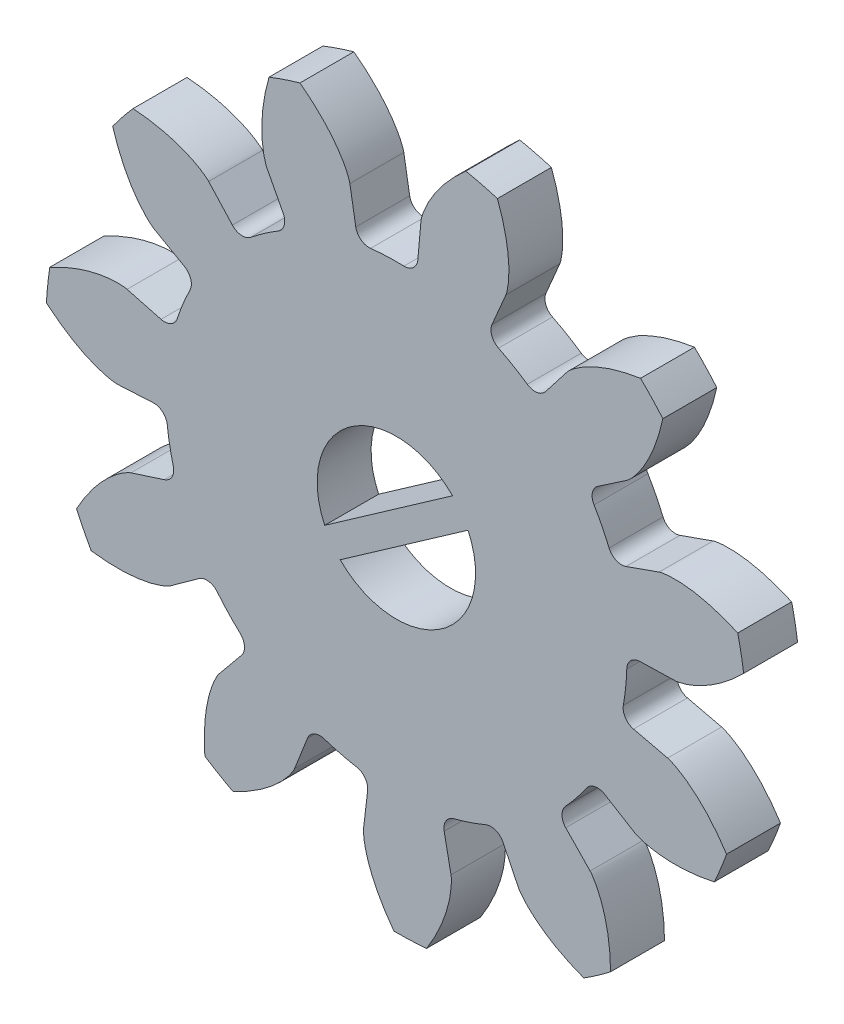
SolidWorks part; units mm, degrees
ref_plane "Front Plane" through (0, 0, 0) normal (0, 0, 1) x (1, 0, 0)
ref_plane "Top Plane" through (0, 0, 0) normal (0, 1, 0) x (1, 0, 0)
ref_plane "Right Plane" through (0, 0, 0) normal (1, 0, 0) x (0, 0, -1)
sketch "Model" plane through (0, 0, 0) normal (0, 0, 1) x (1, 0, 0)
  line L0 (-44.9299, -28.2476) -> (-49.6722, -31.5682)
  line L1 (-49.0986, -32.3873) -> (-44.3563, -29.0667)
  line L2 (-40.6814, -22.148) -> (-41.4798, -23.1761)
  line L3 (-37.9821, -30.0949) -> (-36.6808, -30.0615)
  line L4 (-37.2699, -26.8686) -> (-38.4974, -27.3019)
  line L5 (-39.5362, -25.2471) -> (-38.4595, -24.5155)
  line L6 (-43.4646, -22.0091) -> (-42.9544, -20.8115)
  line L7 (-53.0972, -23.6372) -> (-53.9746, -22.6755)
  line L8 (-55.7432, -27.9864) -> (-57.0012, -27.6517)
  line L9 (-51.8147, -21.1631) -> (-51.2111, -22.3165)
  line L10 (-56.0018, -25.2117) -> (-54.8705, -25.8556)
  line L11 (-55.3922, -36.3718) -> (-54.3365, -35.6103)
  line L12 (-48.0793, -39.2893) -> (-48.2315, -40.5821)
  line L13 (-46.1034, -20.021) -> (-46.2192, -21.3176)
  line L14 (-52.7608, -37.2892) -> (-53.5878, -38.2945)
  line L15 (-50.789, -39.9402) -> (-50.3126, -38.7287)
  line L16 (-55.6178, -33.0756) -> (-56.857, -33.4743)
  line L17 (-57.3355, -30.8812) -> (-56.0356, -30.8114)
  line L18 (-44.9873, -40.4534) -> (-45.2415, -39.1767)
  line L19 (-48.52, -21.4089) -> (-48.7382, -20.1256)
  line L20 (-36.9522, -32.6843) -> (-38.2191, -32.3851)
  line L21 (-39.8292, -37.7485) -> (-40.7332, -36.8119)
  line L22 (-43.0597, -38.4409) -> (-42.4888, -39.6108)
  line L23 (-39.2956, -35.0133) -> (-38.1828, -35.6888)
  arc A0 (-34.1341, -28.5564) -> (-34.3538, -27.3658) centre (-47.0142, -30.3174) ccw
  arc A1 (-39.1252, -27.0231) -> (-38.4974, -27.3019) centre (-38.6639, -26.8304) ccw
  arc A2 (-39.5362, -25.2471) -> (-39.6839, -25.9179) centre (-39.2552, -25.6606) ccw
  arc A3 (-39.1252, -27.0231) -> (-39.6839, -25.9179) centre (-47.0142, -30.3174) ccw
  arc A4 (-37.1309, -21.8724) -> (-37.9593, -20.9896) centre (-47.0142, -30.3174) ccw
  arc A5 (-42.1587, -23.2809) -> (-41.4798, -23.1761) centre (-41.8747, -22.8694) ccw
  arc A6 (-37.9821, -30.0949) -> (-38.469, -30.5794) centre (-37.9693, -30.5947) ccw
  arc A7 (-38.5965, -31.8112) -> (-38.469, -30.5794) centre (-47.0142, -30.3174) ccw
  arc A8 (-43.2655, -17.8697) -> (-44.4398, -17.5749) centre (-47.0142, -30.3174) ccw
  arc A9 (-43.4646, -22.0091) -> (-43.2262, -22.6533) centre (-43.0046, -22.205) ccw
  arc A10 (-54.6701, -26.5127) -> (-55.1395, -27.6587) centre (-47.0142, -30.3174) ccw
  arc A11 (-58.8765, -35.6359) -> (-58.3303, -36.7164) centre (-47.0142, -30.3174) ccw
  arc A12 (-53.0972, -23.6372) -> (-52.4122, -23.6879) centre (-52.7279, -23.3002) ccw
  arc A13 (-55.7432, -27.9864) -> (-55.1395, -27.6587) centre (-55.6147, -27.5032) ccw
  arc A14 (-49.6907, -38.4369) -> (-48.4896, -38.7384) centre (-47.0142, -30.3174) ccw
  arc A15 (-49.6907, -38.4369) -> (-50.3126, -38.7287) centre (-49.8472, -38.9117) ccw
  arc A16 (-51.3978, -22.9776) -> (-52.4122, -23.6879) centre (-47.0142, -30.3174) ccw
  arc A17 (-55.5118, -31.2558) -> (-55.2871, -32.4736) centre (-47.0142, -30.3174) ccw
  arc A18 (-55.5118, -31.2558) -> (-56.0356, -30.8114) centre (-56.0088, -31.3106) ccw
  arc A19 (-48.52, -21.4089) -> (-47.9711, -21.822) centre (-48.027, -21.3251) ccw
  arc A20 (-43.0597, -38.4409) -> (-43.7027, -38.1992) centre (-43.509, -38.6602) ccw
  arc A21 (-42.1587, -23.2809) -> (-43.2262, -22.6533) centre (-47.0142, -30.3174) ccw
  arc A22 (-46.7337, -21.7728) -> (-46.2192, -21.3176) centre (-46.7173, -21.2731) ccw
  arc A23 (-50.5904, -17.819) -> (-51.7376, -18.2059) centre (-47.0142, -30.3174) ccw
  arc A24 (-54.118, -41.2049) -> (-53.0744, -41.8185) centre (-47.0142, -30.3174) ccw
  arc A25 (-55.6178, -33.0756) -> (-55.2871, -32.4736) centre (-55.7709, -32.5997) ccw
  arc A26 (-48.0793, -39.2893) -> (-48.4896, -38.7384) centre (-48.5759, -39.2309) ccw
  arc A27 (-53.6555, -35.7009) -> (-54.3365, -35.6103) centre (-54.0439, -36.0158) ccw
  arc A28 (-56.7799, -21.7365) -> (-57.5358, -22.6822) centre (-47.0142, -30.3174) ccw
  arc A29 (-52.7608, -37.2892) -> (-52.8081, -36.6039) centre (-53.147, -36.9716) ccw
  arc A30 (-46.7337, -21.7728) -> (-47.9711, -21.822) centre (-47.0142, -30.3174) ccw
  arc A31 (-53.6555, -35.7009) -> (-52.8081, -36.6039) centre (-47.0142, -30.3174) ccw
  arc A32 (-51.3978, -22.9776) -> (-51.2111, -22.3165) centre (-51.6541, -22.5483) ccw
  arc A33 (-54.6701, -26.5127) -> (-54.8705, -25.8556) centre (-55.1179, -26.2902) ccw
  arc A34 (-59.8688, -28.3784) -> (-59.9934, -29.5827) centre (-47.0142, -30.3174) ccw
  arc A35 (-44.8761, -38.595) -> (-45.2415, -39.1767) centre (-44.7511, -39.0791) ccw
  arc A36 (-35.2266, -35.7995) -> (-34.7678, -34.6791) centre (-47.0142, -30.3174) ccw
  arc A37 (-40.0617, -41.3021) -> (-39.07, -40.6077) centre (-47.0142, -30.3174) ccw
  arc A38 (-44.8761, -38.595) -> (-43.7027, -38.1992) centre (-47.0142, -30.3174) ccw
  arc A39 (-40.7404, -36.125) -> (-39.9672, -35.1577) centre (-47.0142, -30.3174) ccw
  arc A40 (-40.7404, -36.125) -> (-40.7332, -36.8119) centre (-40.3735, -36.4646) ccw
  arc A41 (-39.2956, -35.0133) -> (-39.9672, -35.1577) centre (-39.555, -35.4408) ccw
  arc A42 (-47.1041, -43.3171) -> (-45.8944, -43.2691) centre (-47.0142, -30.3174) ccw
  arc A43 (-38.5965, -31.8112) -> (-38.2191, -32.3851) centre (-38.1042, -31.8985) ccw
  arc A44 (-44.9299, -28.2476) -> (-49.6722, -31.5682) centre (-47.0142, -30.3174) ccw
  arc A45 (-49.0986, -32.3873) -> (-44.3563, -29.0667) centre (-47.0142, -30.3174) ccw
  spline S0 degree 5 poles (-36.6808, -30.0615) (-36.649, -30.0607) (-36.6095, -30.0571) (-36.555, -30.0476) (-36.4852, -30.0312) (-36.4076, -30.0114) (-36.3299, -29.9907) (-36.2526, -29.9673) (-36.1603, -29.9354) (-36.0686, -29.9002) (-35.9619, -29.8564) (-35.8406, -29.8027) (-35.6978, -29.7326) (-35.5412, -29.6494) (-35.3642, -29.5458) (-35.1677, -29.4197) (-34.9812, -29.2893) (-34.7906, -29.1449) (-34.6101, -28.9978) (-34.4395, -28.8489) (-34.312, -28.7309) (-34.2193, -28.6413) (-34.1602, -28.5826) (-34.1341, -28.5564) knots 0 0 0 0 0 0 0.057143 0.071429 0.1 0.128571 0.142857 0.2 0.214286 0.271429 0.3 0.342857 0.428571 0.485714 0.571429 0.642857 0.728571 0.8 0.871429 0.942857 1 1 1 1 1 1
  spline S1 degree 5 poles (-37.2699, -26.8686) (-37.2399, -26.8581) (-37.2018, -26.8473) (-37.1474, -26.8368) (-37.0764, -26.8271) (-36.9969, -26.8179) (-36.9169, -26.8096) (-36.8363, -26.8038) (-36.7387, -26.8007) (-36.6405, -26.8009) (-36.5252, -26.8037) (-36.3927, -26.8105) (-36.2343, -26.8251) (-36.0583, -26.8469) (-35.856, -26.8806) (-35.6275, -26.9282) (-35.4067, -26.9834) (-35.1771, -27.0503) (-34.956, -27.1233) (-34.7435, -27.2015) (-34.5823, -27.2663) (-34.4637, -27.3169) (-34.3876, -27.3506) (-34.3538, -27.3658) knots 0 0 0 0 0 0 0.057143 0.071429 0.1 0.128571 0.142857 0.2 0.214286 0.271429 0.3 0.342857 0.428571 0.485714 0.571429 0.642857 0.728571 0.8 0.871429 0.942857 1 1 1 1 1 1
  spline S2 degree 5 poles (-40.6814, -22.148) (-40.6618, -22.1228) (-40.6356, -22.0932) (-40.5955, -22.0549) (-40.541, -22.0084) (-40.4791, -21.9577) (-40.4163, -21.9074) (-40.3516, -21.859) (-40.2712, -21.8037) (-40.1885, -21.7506) (-40.0899, -21.6907) (-39.9748, -21.6248) (-39.8336, -21.5514) (-39.6738, -21.4746) (-39.4854, -21.3936) (-39.2674, -21.3101) (-39.0519, -21.2372) (-38.8226, -21.1693) (-38.597, -21.1112) (-38.376, -21.0621) (-38.2054, -21.0294) (-38.0783, -21.0079) (-37.996, -20.9951) (-37.9593, -20.9896) knots 0 0 0 0 0 0 0.057143 0.071429 0.1 0.128571 0.142857 0.2 0.214286 0.271429 0.3 0.342857 0.428571 0.485714 0.571429 0.642857 0.728571 0.8 0.871429 0.942857 1 1 1 1 1 1
  spline S3 degree 5 poles (-38.4595, -24.5155) (-38.4332, -24.4976) (-38.402, -24.4732) (-38.3612, -24.4357) (-38.3114, -24.3843) (-38.2568, -24.3256) (-38.2027, -24.2662) (-38.1502, -24.2047) (-38.0899, -24.128) (-38.0317, -24.0488) (-37.9657, -23.9542) (-37.8926, -23.8435) (-37.8105, -23.7073) (-37.7236, -23.5527) (-37.6308, -23.3698) (-37.5337, -23.1575) (-37.4473, -22.947) (-37.365, -22.7225) (-37.2927, -22.5011) (-37.2296, -22.2836) (-37.1862, -22.1154) (-37.1567, -21.9899) (-37.1387, -21.9086) (-37.1309, -21.8724) knots 0 0 0 0 0 0 0.057143 0.071429 0.1 0.128571 0.142857 0.2 0.214286 0.271429 0.3 0.342857 0.428571 0.485714 0.571429 0.642857 0.728571 0.8 0.871429 0.942857 1 1 1 1 1 1
  spline S4 degree 5 poles (-53.9746, -22.6755) (-53.9961, -22.652) (-54.0246, -22.6246) (-54.0675, -22.5896) (-54.1256, -22.5476) (-54.1914, -22.5019) (-54.2579, -22.4568) (-54.3262, -22.4136) (-54.4108, -22.3648) (-54.4974, -22.3185) (-54.6004, -22.2666) (-54.7204, -22.21) (-54.8669, -22.1481) (-55.0323, -22.0841) (-55.2266, -22.0183) (-55.4505, -21.9524) (-55.6712, -21.8968) (-55.9051, -21.8473) (-56.1345, -21.8072) (-56.3587, -21.7758) (-56.5315, -21.7567) (-56.6599, -21.7453) (-56.7429, -21.7391) (-56.7799, -21.7365) knots 0 0 0 0 0 0 0.057143 0.071429 0.1 0.128571 0.142857 0.2 0.214286 0.271429 0.3 0.342857 0.428571 0.485714 0.571429 0.642857 0.728571 0.8 0.871429 0.942857 1 1 1 1 1 1
  spline S5 degree 5 poles (-48.7382, -20.1256) (-48.7435, -20.0942) (-48.7527, -20.0557) (-48.7699, -20.003) (-48.796, -19.9363) (-48.8266, -19.8623) (-48.8582, -19.7884) (-48.8923, -19.7151) (-48.9371, -19.6284) (-48.985, -19.5426) (-49.0435, -19.4432) (-49.1139, -19.3308) (-49.2037, -19.1994) (-49.3082, -19.0562) (-49.436, -18.8958) (-49.5888, -18.7193) (-49.7444, -18.5532) (-49.9144, -18.3851) (-50.0858, -18.2274) (-50.2574, -18.0797) (-50.3924, -17.9703) (-50.4942, -17.8913) (-50.5607, -17.8412) (-50.5904, -17.819) knots 0 0 0 0 0 0 0.057143 0.071429 0.1 0.128571 0.142857 0.2 0.214286 0.271429 0.3 0.342857 0.428571 0.485714 0.571429 0.642857 0.728571 0.8 0.871429 0.942857 1 1 1 1 1 1
  spline S6 degree 5 poles (-57.3355, -30.8812) (-57.3673, -30.8829) (-57.4068, -30.8825) (-57.462, -30.8773) (-57.5328, -30.8666) (-57.6118, -30.853) (-57.6908, -30.8385) (-57.7698, -30.8213) (-57.8643, -30.7967) (-57.9585, -30.7689) (-58.0683, -30.7337) (-58.1935, -30.6899) (-58.3414, -30.6312) (-58.5042, -30.5608) (-58.6888, -30.4714) (-58.8946, -30.3613) (-59.0909, -30.2462) (-59.2923, -30.1173) (-59.4839, -29.985) (-59.6658, -29.8501) (-59.8022, -29.7425) (-59.9017, -29.6605) (-59.9653, -29.6068) (-59.9934, -29.5827) knots 0 0 0 0 0 0 0.057143 0.071429 0.1 0.128571 0.142857 0.2 0.214286 0.271429 0.3 0.342857 0.428571 0.485714 0.571429 0.642857 0.728571 0.8 0.871429 0.942857 1 1 1 1 1 1
  spline S7 degree 5 poles (-50.789, -39.9402) (-50.8006, -39.9698) (-50.8175, -40.0056) (-50.8451, -40.0536) (-50.8843, -40.1136) (-50.9295, -40.1798) (-50.9755, -40.2456) (-51.0239, -40.3103) (-51.0855, -40.3861) (-51.15, -40.4603) (-51.2276, -40.5455) (-51.3195, -40.6412) (-51.4343, -40.7514) (-51.566, -40.8701) (-51.7239, -41.0009) (-51.9096, -41.1425) (-52.0959, -41.2731) (-52.2968, -41.4028) (-52.4968, -41.5222) (-52.695, -41.6315) (-52.8495, -41.711) (-52.9654, -41.7674) (-53.0407, -41.8029) (-53.0744, -41.8185) knots 0 0 0 0 0 0 0.057143 0.071429 0.1 0.128571 0.142857 0.2 0.214286 0.271429 0.3 0.342857 0.428571 0.485714 0.571429 0.642857 0.728571 0.8 0.871429 0.942857 1 1 1 1 1 1
  spline S8 degree 5 poles (-46.1034, -20.021) (-46.1006, -19.9893) (-46.0945, -19.9502) (-46.0815, -19.8964) (-46.0608, -19.8278) (-46.0361, -19.7516) (-46.0105, -19.6754) (-45.9823, -19.5997) (-45.9445, -19.5096) (-45.9036, -19.4203) (-45.8531, -19.3166) (-45.7919, -19.1989) (-45.7128, -19.0609) (-45.6199, -18.9098) (-45.5052, -18.7398) (-45.3669, -18.5517) (-45.225, -18.3739) (-45.0688, -18.1928) (-44.9105, -18.022) (-44.7511, -17.8612) (-44.6252, -17.7414) (-44.5299, -17.6546) (-44.4677, -17.5993) (-44.4398, -17.5749) knots 0 0 0 0 0 0 0.057143 0.071429 0.1 0.128571 0.142857 0.2 0.214286 0.271429 0.3 0.342857 0.428571 0.485714 0.571429 0.642857 0.728571 0.8 0.871429 0.942857 1 1 1 1 1 1
  spline S9 degree 5 poles (-51.8147, -21.1631) (-51.8294, -21.1349) (-51.8455, -21.0987) (-51.8637, -21.0464) (-51.8833, -20.9775) (-51.9037, -20.9001) (-51.9234, -20.8221) (-51.9406, -20.7431) (-51.9575, -20.647) (-51.9714, -20.5497) (-51.985, -20.4352) (-51.9971, -20.3031) (-52.0051, -20.1442) (-52.0087, -19.9669) (-52.0041, -19.7619) (-51.9895, -19.5289) (-51.9662, -19.3025) (-51.9327, -19.0658) (-51.8919, -18.8365) (-51.8448, -18.615) (-51.8036, -18.4462) (-51.7704, -18.3217) (-51.7479, -18.2415) (-51.7376, -18.2059) knots 0 0 0 0 0 0 0.057143 0.071429 0.1 0.128571 0.142857 0.2 0.214286 0.271429 0.3 0.342857 0.428571 0.485714 0.571429 0.642857 0.728571 0.8 0.871429 0.942857 1 1 1 1 1 1
  spline S10 degree 5 poles (-56.857, -33.4743) (-56.8873, -33.484) (-56.9241, -33.4986) (-56.9738, -33.5231) (-57.0361, -33.5584) (-57.105, -33.5993) (-57.1737, -33.641) (-57.2413, -33.6853) (-57.3208, -33.7419) (-57.399, -33.8015) (-57.489, -33.8736) (-57.5902, -33.9593) (-57.7075, -34.0668) (-57.8344, -34.1907) (-57.9749, -34.34) (-58.1279, -34.5164) (-58.2702, -34.694) (-58.4123, -34.8862) (-58.5441, -35.0783) (-58.6659, -35.2692) (-58.7549, -35.4184) (-58.8186, -35.5304) (-58.8588, -35.6034) (-58.8765, -35.6359) knots 0 0 0 0 0 0 0.057143 0.071429 0.1 0.128571 0.142857 0.2 0.214286 0.271429 0.3 0.342857 0.428571 0.485714 0.571429 0.642857 0.728571 0.8 0.871429 0.942857 1 1 1 1 1 1
  spline S11 degree 5 poles (-55.3922, -36.3718) (-55.418, -36.3904) (-55.4516, -36.4115) (-55.5007, -36.4369) (-55.5661, -36.4662) (-55.6399, -36.4974) (-55.7143, -36.5279) (-55.79, -36.5562) (-55.8827, -36.5866) (-55.9771, -36.6142) (-56.0885, -36.644) (-56.2175, -36.6747) (-56.3736, -36.7053) (-56.5486, -36.7341) (-56.7522, -36.7587) (-56.9849, -36.7774) (-57.2123, -36.7866) (-57.4514, -36.7871) (-57.6842, -36.7794) (-57.9101, -36.7642) (-58.083, -36.7475) (-58.211, -36.7323) (-58.2936, -36.7215) (-58.3303, -36.7164) knots 0 0 0 0 0 0 0.057143 0.071429 0.1 0.128571 0.142857 0.2 0.214286 0.271429 0.3 0.342857 0.428571 0.485714 0.571429 0.642857 0.728571 0.8 0.871429 0.942857 1 1 1 1 1 1
  spline S12 degree 5 poles (-57.0012, -27.6517) (-57.032, -27.6435) (-57.0708, -27.6359) (-57.1258, -27.6297) (-57.1974, -27.6257) (-57.2774, -27.6228) (-57.3578, -27.6208) (-57.4386, -27.6215) (-57.5361, -27.6261) (-57.6341, -27.634) (-57.7488, -27.646) (-57.8803, -27.6633) (-58.037, -27.6904) (-58.2108, -27.726) (-58.4097, -27.7757) (-58.6338, -27.8413) (-58.8495, -27.9138) (-59.073, -27.9987) (-59.2877, -28.089) (-59.4933, -28.1838) (-59.6489, -28.2611) (-59.7631, -28.321) (-59.8363, -28.3606) (-59.8688, -28.3784) knots 0 0 0 0 0 0 0.057143 0.071429 0.1 0.128571 0.142857 0.2 0.214286 0.271429 0.3 0.342857 0.428571 0.485714 0.571429 0.642857 0.728571 0.8 0.871429 0.942857 1 1 1 1 1 1
  spline S13 degree 5 poles (-42.9544, -20.8115) (-42.9419, -20.7822) (-42.9288, -20.7448) (-42.9148, -20.6913) (-42.9007, -20.621) (-42.8864, -20.5422) (-42.873, -20.4629) (-42.8622, -20.3828) (-42.8529, -20.2857) (-42.8468, -20.1876) (-42.8423, -20.0724) (-42.8407, -19.9397) (-42.8453, -19.7807) (-42.8558, -19.6037) (-42.8766, -19.3996) (-42.9096, -19.1685) (-42.9507, -18.9447) (-43.0029, -18.7114) (-43.0618, -18.486) (-43.1263, -18.269) (-43.1808, -18.104) (-43.2237, -17.9825) (-43.2525, -17.9044) (-43.2655, -17.8697) knots 0 0 0 0 0 0 0.057143 0.071429 0.1 0.128571 0.142857 0.2 0.214286 0.271429 0.3 0.342857 0.428571 0.485714 0.571429 0.642857 0.728571 0.8 0.871429 0.942857 1 1 1 1 1 1
  spline S14 degree 5 poles (-56.0018, -25.2117) (-56.0295, -25.1959) (-56.0625, -25.1741) (-56.1061, -25.14) (-56.1599, -25.0926) (-56.219, -25.0385) (-56.2776, -24.9836) (-56.3348, -24.9264) (-56.401, -24.8547) (-56.4653, -24.7803) (-56.5386, -24.6914) (-56.6202, -24.5868) (-56.7129, -24.4575) (-56.8117, -24.3102) (-56.9187, -24.1353) (-57.0324, -23.9314) (-57.1352, -23.7284) (-57.235, -23.5111) (-57.3247, -23.2961) (-57.4047, -23.0843) (-57.4613, -22.9201) (-57.5007, -22.7973) (-57.5251, -22.7177) (-57.5358, -22.6822) knots 0 0 0 0 0 0 0.057143 0.071429 0.1 0.128571 0.142857 0.2 0.214286 0.271429 0.3 0.342857 0.428571 0.485714 0.571429 0.642857 0.728571 0.8 0.871429 0.942857 1 1 1 1 1 1
  spline S15 degree 5 poles (-53.5878, -38.2945) (-53.608, -38.3191) (-53.6311, -38.3513) (-53.6596, -38.3987) (-53.693, -38.4622) (-53.7288, -38.5338) (-53.764, -38.6061) (-53.797, -38.6798) (-53.8333, -38.7705) (-53.8668, -38.8629) (-53.9035, -38.9722) (-53.9424, -39.099) (-53.9829, -39.2528) (-54.0227, -39.4257) (-54.0602, -39.6273) (-54.0936, -39.8583) (-54.1172, -40.0846) (-54.1329, -40.3233) (-54.1399, -40.5561) (-54.1391, -40.7824) (-54.1333, -40.9561) (-54.1264, -41.0848) (-54.1207, -41.1679) (-54.118, -41.2049) knots 0 0 0 0 0 0 0.057143 0.071429 0.1 0.128571 0.142857 0.2 0.214286 0.271429 0.3 0.342857 0.428571 0.485714 0.571429 0.642857 0.728571 0.8 0.871429 0.942857 1 1 1 1 1 1
  spline S16 degree 5 poles (-48.2315, -40.5821) (-48.2352, -40.6138) (-48.2373, -40.6533) (-48.2356, -40.7086) (-48.2294, -40.78) (-48.2208, -40.8597) (-48.2114, -40.9395) (-48.1992, -41.0194) (-48.1807, -41.1152) (-48.159, -41.2111) (-48.1308, -41.3229) (-48.095, -41.4506) (-48.0458, -41.6019) (-47.9858, -41.7688) (-47.9084, -41.9587) (-47.8115, -42.1711) (-47.7091, -42.3743) (-47.5932, -42.5835) (-47.4733, -42.7831) (-47.3502, -42.9732) (-47.2515, -43.1161) (-47.176, -43.2207) (-47.1264, -43.2875) (-47.1041, -43.3171) knots 0 0 0 0 0 0 0.057143 0.071429 0.1 0.128571 0.142857 0.2 0.214286 0.271429 0.3 0.342857 0.428571 0.485714 0.571429 0.642857 0.728571 0.8 0.871429 0.942857 1 1 1 1 1 1
  spline S17 degree 5 poles (-39.8292, -37.7485) (-39.8071, -37.7714) (-39.7815, -37.8016) (-39.7493, -37.8467) (-39.711, -37.9073) (-39.6696, -37.9758) (-39.6288, -38.0451) (-39.5901, -38.116) (-39.5467, -38.2035) (-39.506, -38.2929) (-39.4607, -38.399) (-39.4119, -38.5223) (-39.3594, -38.6725) (-39.306, -38.8416) (-39.2526, -39.0396) (-39.2011, -39.2673) (-39.1596, -39.491) (-39.125, -39.7276) (-39.0996, -39.9591) (-39.0824, -40.1849) (-39.0744, -40.3585) (-39.0712, -40.4873) (-39.0702, -40.5706) (-39.07, -40.6077) knots 0 0 0 0 0 0 0.057143 0.071429 0.1 0.128571 0.142857 0.2 0.214286 0.271429 0.3 0.342857 0.428571 0.485714 0.571429 0.642857 0.728571 0.8 0.871429 0.942857 1 1 1 1 1 1
  spline S18 degree 5 poles (-36.9522, -32.6843) (-36.9213, -32.6916) (-36.8834, -32.7032) (-36.832, -32.7237) (-36.767, -32.754) (-36.6951, -32.7893) (-36.6233, -32.8255) (-36.5524, -32.8642) (-36.4687, -32.9144) (-36.3861, -32.9676) (-36.2906, -33.0323) (-36.1829, -33.1097) (-36.0575, -33.2076) (-35.9212, -33.321) (-35.7692, -33.4588) (-35.6027, -33.6224) (-35.4469, -33.7882) (-35.2899, -33.9686) (-35.1433, -34.1496) (-35.0068, -34.3302) (-34.9062, -34.4719) (-34.8338, -34.5785) (-34.788, -34.648) (-34.7678, -34.6791) knots 0 0 0 0 0 0 0.057143 0.071429 0.1 0.128571 0.142857 0.2 0.214286 0.271429 0.3 0.342857 0.428571 0.485714 0.571429 0.642857 0.728571 0.8 0.871429 0.942857 1 1 1 1 1 1
  spline S19 degree 5 poles (-44.9873, -40.4534) (-44.9811, -40.4846) (-44.9759, -40.5238) (-44.9732, -40.5792) (-44.9738, -40.6508) (-44.976, -40.7309) (-44.9791, -40.8112) (-44.9848, -40.8918) (-44.9957, -40.9888) (-45.0098, -41.0861) (-45.029, -41.1998) (-45.0546, -41.3299) (-45.0916, -41.4847) (-45.1382, -41.6558) (-45.2003, -41.8512) (-45.28, -42.0706) (-45.3661, -42.2813) (-45.465, -42.499) (-45.5687, -42.7075) (-45.6763, -42.9067) (-45.7634, -43.0571) (-45.8304, -43.1672) (-45.8745, -43.2378) (-45.8944, -43.2691) knots 0 0 0 0 0 0 0.057143 0.071429 0.1 0.128571 0.142857 0.2 0.214286 0.271429 0.3 0.342857 0.428571 0.485714 0.571429 0.642857 0.728571 0.8 0.871429 0.942857 1 1 1 1 1 1
  spline S20 degree 5 poles (-38.1828, -35.6888) (-38.1556, -35.7053) (-38.1205, -35.7236) (-38.0694, -35.7451) (-38.0019, -35.7691) (-37.9259, -35.7944) (-37.8494, -35.8189) (-37.7717, -35.8411) (-37.6768, -35.8641) (-37.5806, -35.8841) (-37.4672, -35.9049) (-37.3361, -35.9254) (-37.178, -35.9435) (-37.0013, -35.9583) (-36.7964, -35.9667) (-36.563, -35.9669) (-36.3356, -35.9581) (-36.0972, -35.9396) (-35.8657, -35.9135) (-35.6418, -35.8805) (-35.4707, -35.85) (-35.3443, -35.8248) (-35.2629, -35.8074) (-35.2266, -35.7995) knots 0 0 0 0 0 0 0.057143 0.071429 0.1 0.128571 0.142857 0.2 0.214286 0.271429 0.3 0.342857 0.428571 0.485714 0.571429 0.642857 0.728571 0.8 0.871429 0.942857 1 1 1 1 1 1
  spline S21 degree 5 poles (-42.4888, -39.6108) (-42.4748, -39.6394) (-42.4552, -39.6737) (-42.4238, -39.7194) (-42.38, -39.7761) (-42.3297, -39.8385) (-42.2786, -39.9005) (-42.2252, -39.9611) (-42.1578, -40.0318) (-42.0877, -40.1006) (-42.0035, -40.1795) (-41.9044, -40.2675) (-41.7812, -40.3682) (-41.6405, -40.4762) (-41.4727, -40.5941) (-41.2764, -40.7205) (-41.0803, -40.8359) (-40.8698, -40.9493) (-40.661, -41.0524) (-40.4547, -41.1458) (-40.2943, -41.2127) (-40.1743, -41.2598) (-40.0965, -41.2892) (-40.0617, -41.3021) knots 0 0 0 0 0 0 0.057143 0.071429 0.1 0.128571 0.142857 0.2 0.214286 0.271429 0.3 0.342857 0.428571 0.485714 0.571429 0.642857 0.728571 0.8 0.871429 0.942857 1 1 1 1 1 1
extrude "Boss-Extrude1" add sketch "Model" along normal blind 2
